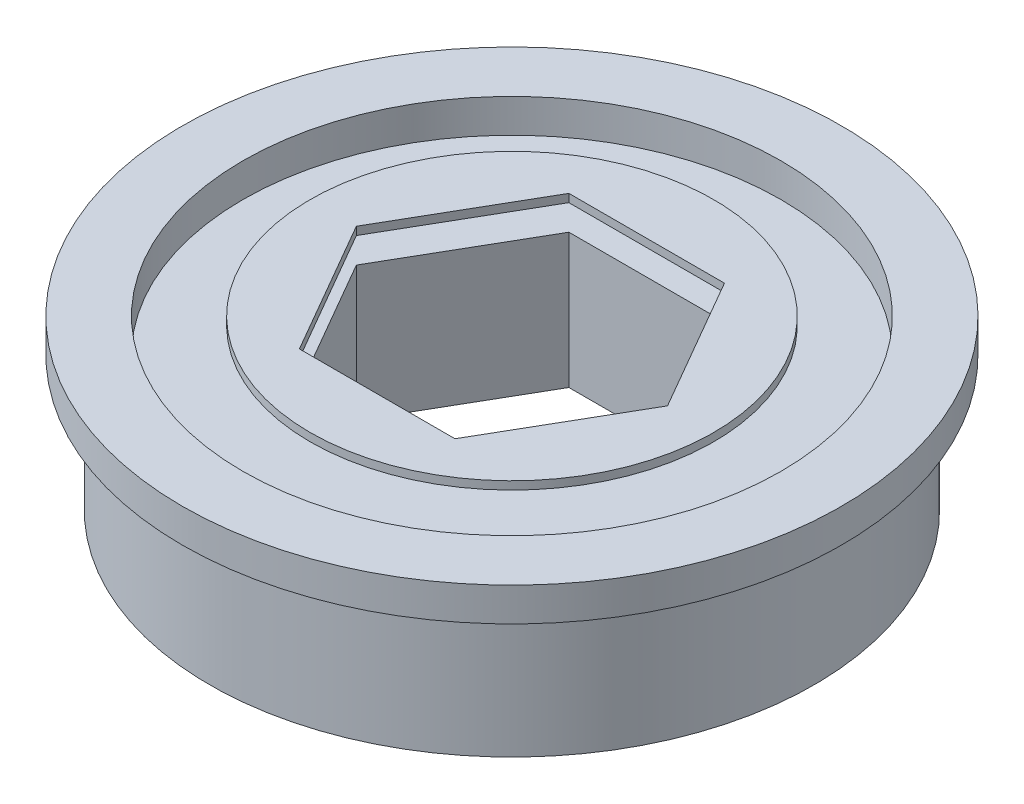
SolidWorks part; units mm, degrees
ref_plane "Front Plane" through (0, 0, 0) normal (0, 0, 1) x (1, 0, 0)
ref_plane "Top Plane" through (0, 0, 0) normal (0, 1, 0) x (1, 0, 0)
ref_plane "Right Plane" through (0, 0, 0) normal (1, 0, 0) x (0, 0, -1)
ref_plane "Plane1" through (0, 0, 0) normal (0, 0, -1) x (-1, 0, 0)
sketch "Sketch1" plane through (0, 0, 0) normal (0, 0, -1) x (-1, 0, 0)
  line L0 (-15.5575, 6.35) -> (0, 6.35)
  line L1 (0, 6.35) -> (0, 7.9375)
  line L2 (0, 7.9375) -> (-15.5575, 7.9375)
  line L3 (-15.5575, 7.9375) -> (-15.5575, 6.35)
  line L4 (0, 6.35) -> (0, 7.9375) construction
revolve "Revolve1" add sketch "Sketch1" angle 360 about L4
hole_wizard "1 (1) Diameter Hole1" positions "Sketch3" profile "Sketch2" hole size "1" standard "ANSI Inch"
sketch "Sketch3" plane through (0, 7.9375, 0) normal (0, 1, 0) x (1, 0, 0)
  point P0 (0, 0)
sketch "Sketch2" plane through (0, 7.9375, 0) normal (1, 0, 0) x (0, 0, 1)
  line L0 (0, 0) -> (0, 1.5875)
  line L1 (0, 1.5875) -> (12.7, 1.5875)
  line L2 (12.7, 1.5875) -> (12.7, 0)
  line L5 (12.7, 0) -> (0, 0)
  line L11 (0, -6.35) -> (0, 107.95) construction
  dimension "Thru Hole Dia." = 25.4
  dimension "Thru Hole Depth" = 1.5875
ref_plane "Plane2" through (0, 7.5565, 0) normal (0, -1, 0) x (1, 0, 0)
sketch "Sketch4" plane through (0, 7.5565, 0) normal (0, -1, 0) x (1, 0, 0)
  circle A0 centre (0, 0) radius 9.525
extrude "Boss-Extrude1" add sketch "Sketch4" against normal blind 0.381
sketch "Sketch5" plane through (0, 6.35, 0) normal (0, -1, 0) x (1, 0, 0)
  circle A0 centre (0, 0) radius 14.2748
extrude "Boss-Extrude2" add sketch "Sketch5" along normal blind 6.35
sketch "Sketch6" plane through (0, 0, 0) normal (0, -1, 0) x (1, 0, 0)
  line L0 (-3.6719, 6.36) -> (-7.3439, 0)
  line L1 (-7.3439, 0) -> (-3.6719, -6.36)
  line L2 (-3.6719, -6.36) -> (3.6719, -6.36)
  line L3 (3.6719, -6.36) -> (7.3439, 0)
  line L4 (7.3439, 0) -> (3.6719, 6.36)
  line L5 (3.6719, 6.36) -> (-3.6719, 6.36)
extrude "Cut-Extrude1" cut sketch "Sketch6" against normal through all
